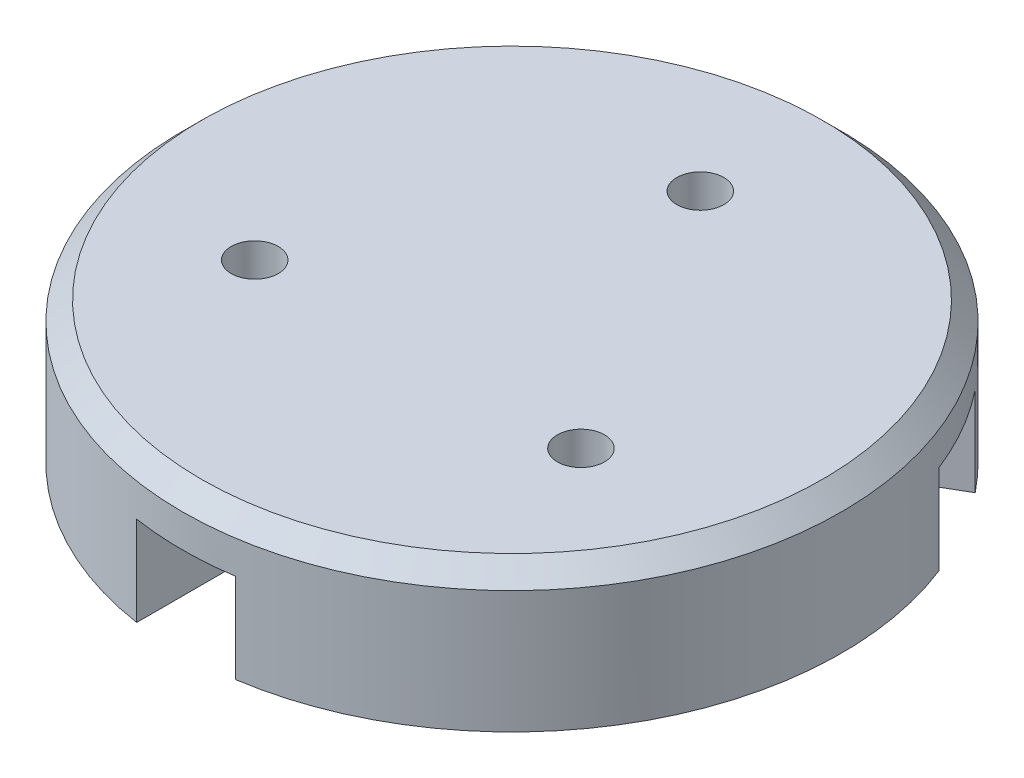
SolidWorks part; units mm, degrees
ref_plane "Спереди" through (0, 0, 0) normal (0, 0, 1) x (1, 0, 0)
ref_plane "Сверху" through (0, 0, 0) normal (0, 1, 0) x (1, 0, 0)
ref_plane "Справа" through (0, 0, 0) normal (1, 0, 0) x (0, 0, -1)
sketch "Эскиз1" plane through (0, 0, 0) normal (0, 1, 0) x (1, 0, 0)
  circle A0 centre (0, 0) radius 7
extrude "Бобышка-Вытянуть1" add sketch "Эскиз1" along normal blind 3
sketch "Эскиз2" plane through (0, 0, 0) normal (0, -1, 0) x (1, 0, 0)
  line L0 (10.9172, -5.0907) -> (9.8672, -6.9094)
  line L1 (-1.0501, 12) -> (1.0499, 12)
  line L2 (-1.0501, 12) -> (-1.0501, 2)
  line L3 (-1.0501, 2) -> (1.0499, 2)
  line L4 (1.0499, 12) -> (1.0499, 2)
  line L5 (10.9172, -5.0907) -> (2.257, -0.0907)
  line L6 (2.257, -0.0907) -> (1.207, -1.9094)
  line L7 (9.8672, -6.9094) -> (1.207, -1.9094)
  line L8 (-9.8674, -6.9094) -> (-10.9174, -5.0907)
  line L9 (-9.8674, -6.9094) -> (-1.2071, -1.9094)
  line L10 (-1.2071, -1.9094) -> (-2.2571, -0.0907)
  line L11 (-10.9174, -5.0907) -> (-2.2571, -0.0907)
  point P13 (-0.0001, 0)
  dimension "D1" = 2.1
  dimension "D2" = 10
extrude "Вырез-Вытянуть1" cut sketch "Эскиз2" against normal blind 1.9
sketch "Эскиз3" plane through (0, 0, 0) normal (0, -1, 0) x (1, 0, 0)
  circle A0 centre (0, 0) radius 1.05
extrude "Вырез-Вытянуть2" cut sketch "Эскиз3" against normal blind 2.5 and the other way through all
sketch "Эскиз4" plane through (0, 0, 0) normal (0, -1, 0) x (1, 0, 0)
  circle A0 centre (0, -4) radius 0.5
  circle A1 centre (-3.4641, 2) radius 0.5
  circle A2 centre (3.4641, 2) radius 0.5
  point P10 (0, 0)
  dimension "D1" = 4
  dimension "D3" = 1
  dimension "D2" = 3
extrude "Вырез-Вытянуть3" cut sketch "Эскиз4" against normal through all both and the other way through all
chamfer "Фаска1" distance 0.4 angle 45 1 edges at (0, 3, 7)
